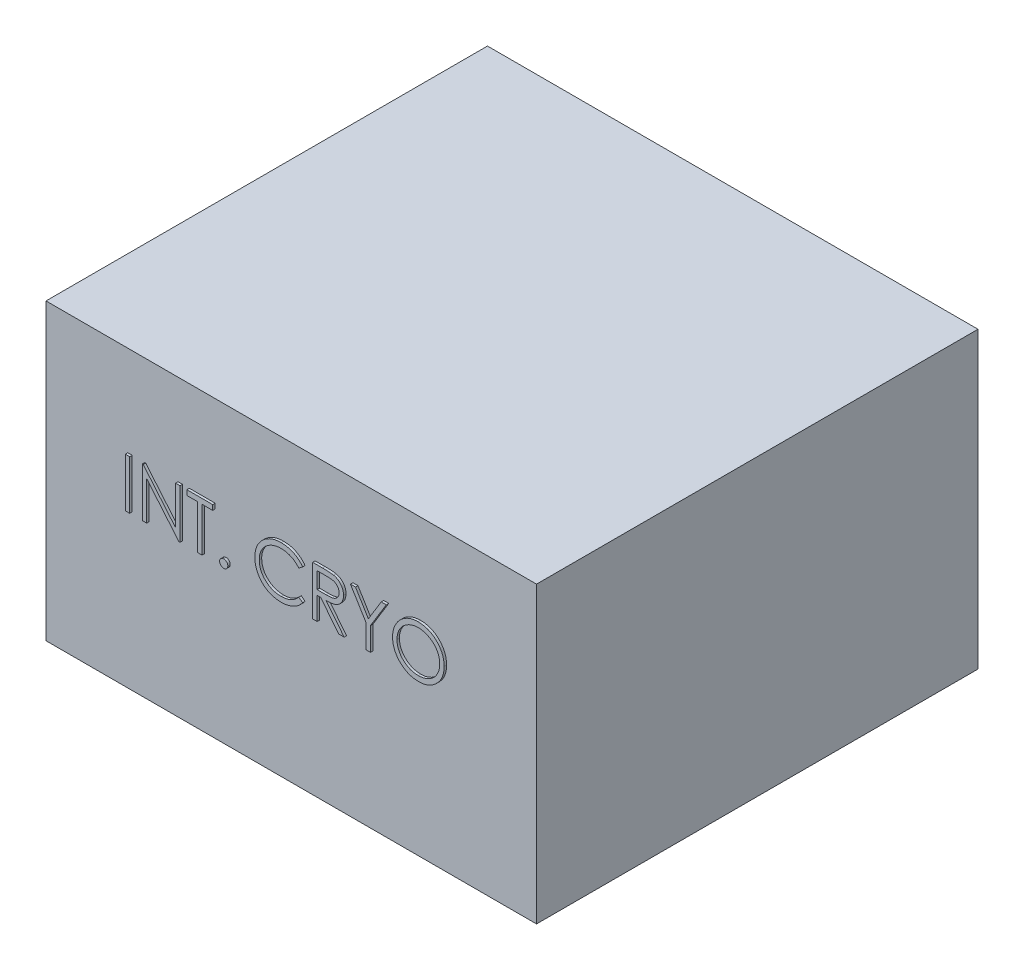
SolidWorks part; units mm, degrees
ref_plane "Front Plane" through (0, 0, 0) normal (0, 0, 1) x (1, 0, 0)
ref_plane "Top Plane" through (0, 0, 0) normal (0, 1, 0) x (1, 0, 0)
ref_plane "Right Plane" through (0, 0, 0) normal (1, 0, 0) x (0, 0, -1)
sketch "Sketch1" plane through (0, 0, 0) normal (0, 0, 1) x (1, 0, 0)
  line L1 (0, 0) -> (-1000, 0)
  line L2 (0, 0) -> (0, -600)
  line L3 (0, -600) -> (-1000, -600)
  line L4 (-1000, 0) -> (-1000, -600)
  dimension "D1" = 1000
  dimension "D2" = 600
extrude "Boss-Extrude1" add sketch "Sketch1" along normal blind 900
sketch "Sketch2" plane through (0, 0, 900) normal (0, 0, 1) x (1, 0, 0)
  line L0 (-1000, -284.6692) -> (0, -284.6692) construction
  line L1 (-1000, 0) -> (-1000, -600) construction
  line L2 (0, -600) -> (0, 0) construction
  text T0 "    INT. CRYO" font "Century Gothic" height 100
extrude "Boss-Extrude2" add sketch "Sketch2" along normal blind 5
